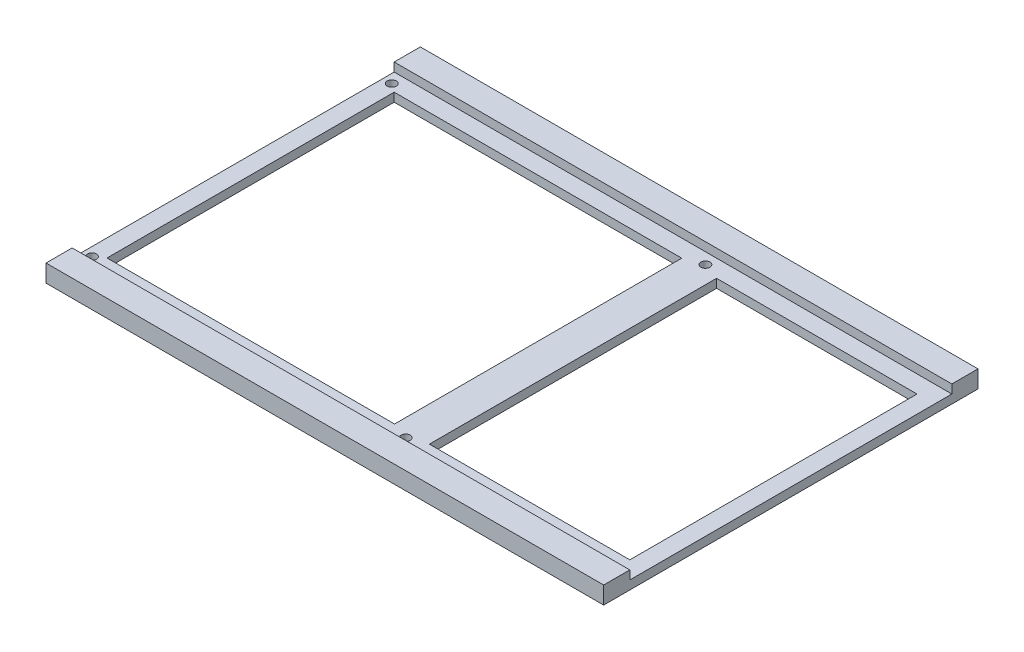
SolidWorks part; units mm, degrees
ref_plane "Front Plane" through (0, 0, 0) normal (0, 0, 1) x (1, 0, 0)
ref_plane "Top Plane" through (0, 0, 0) normal (0, 1, 0) x (1, 0, 0)
ref_plane "Right Plane" through (0, 0, 0) normal (1, 0, 0) x (0, 0, -1)
sketch "Sketch1" plane through (0, 0, 0) normal (0, 1, 0) x (1, 0, 0)
  line L1 (101.6, -68.199) -> (-101.6, -68.199)
  line L2 (101.6, -68.199) -> (101.6, 68.199)
  line L3 (101.6, 68.199) -> (-101.6, 68.199)
  line L4 (-101.6, -68.199) -> (-101.6, 68.199)
  line L5 (101.6, -68.199) -> (-101.6, 68.199) construction
  line L6 (101.6, 68.199) -> (-101.6, -68.199) construction
  point P0 (0, 0)
  dimension "D1" = 203.2
  dimension "D2" = 136.398
extrude "Boss-Extrude1" add sketch "Sketch1" along normal blind 6.35
sketch "Sketch3" plane through (101.6, 0, 0) normal (1, 0, 0) x (0, 0, -1)
  line L0 (-68.199, 6.35) -> (68.199, 6.35) construction
  line L1 (58.674, 3.175) -> (-58.674, 3.175)
  line L2 (58.674, 3.175) -> (58.674, 6.35)
  line L3 (58.674, 6.35) -> (-58.674, 6.35)
  line L4 (-58.674, 3.175) -> (-58.674, 6.35)
  line L5 (58.674, 3.175) -> (-58.674, 6.35) construction
  line L6 (58.674, 6.35) -> (-58.674, 3.175) construction
  line L7 (-68.199, 0) -> (68.199, 0) construction
  line L8 (-68.199, 6.35) -> (-68.199, 0) construction
  point P0 (0, 4.7625)
  point P10 (0, 0)
  dimension "D1" = 9.525
  dimension "D2" = 3.175
extrude "Cut-Extrude1" cut sketch "Sketch3" against normal through all
sketch "Sketch4" plane through (0, 3.175, 0) normal (0, 1, 0) x (1, 0, 0)
  line L1 (-101.6, -58.674) -> (-101.6, 58.674) construction
  line L2 (95.25, -52.324) -> (-95.25, -52.324)
  line L3 (95.25, -52.324) -> (95.25, 52.324)
  line L4 (95.25, 52.324) -> (-95.25, 52.324)
  line L5 (-95.25, -52.324) -> (-95.25, 52.324)
  line L6 (95.25, -52.324) -> (-95.25, 52.324) construction
  line L7 (95.25, 52.324) -> (-95.25, -52.324) construction
  line L8 (-101.6, 58.674) -> (101.6, 58.674) construction
  line L9 (22.225, -52.324) -> (22.225, 52.324)
  line L10 (9.525, -52.324) -> (9.525, 52.324)
  line L11 (-101.6, -11.9685) -> (-95.25, -11.9685) construction
  line L12 (9.525, 38.4482) -> (22.225, 38.4482) construction
  line L13 (15.875, 38.4482) -> (15.875, -96.3543) construction
  line L14 (-98.425, -11.9685) -> (-98.425, 16.517) construction
  point P0 (0, 0)
  dimension "D1" = 6.35
  dimension "D2" = 6.35
  dimension "D3" = 12.7
  dimension "D4" = 114.3
extrude "Cut-Extrude3" cut sketch "Sketch4" against normal through all contours L2 L10 L4 L5 | L9 L2 L3 L4
hole_wizard "M4x0.7 Tapped Hole1" positions "Sketch6" profile "Sketch5" tap size "M4x0.7" standard "ANSI Metric"
sketch "Sketch6" plane through (0, 3.175, 0) normal (0, 1, 0) x (1, 0, 0)
  line L0 (-98.425, -54.61) -> (-98.425, 54.61) construction
  line L2 (-95.25, -65.1111) -> (-101.6, -65.1111) construction
  line L3 (-95.25, -52.324) -> (-95.25, 52.324) construction
  line L4 (-101.6, -58.674) -> (-101.6, 58.674) construction
  line L5 (15.875, 54.61) -> (15.875, -54.61) construction
  line L7 (9.525, 0) -> (22.225, 0) construction
  line L8 (9.525, -52.324) -> (9.525, 52.324) construction
  line L9 (22.225, -52.324) -> (22.225, 52.324) construction
  point P0 (-98.425, -54.61)
  point P2 (-98.425, 54.61)
  point P9 (-98.425, 0)
  point P19 (-98.425, -65.1111)
  point P20 (15.875, 54.61)
  point P22 (15.875, -54.61)
  point P37 (15.875, 0)
  dimension "D1" = 109.22
sketch "Sketch5" plane through (-98.425, 3.175, 54.61) normal (1, 0, 0) x (0, 0, 1)
  line L0 (0, 0) -> (0, 9.906)
  line L1 (0, 9.906) -> (1.65, 9.906)
  line L2 (1.65, 9.906) -> (1.65, 0)
  line L5 (1.65, 0) -> (0, 0)
  line L10 (0, 9.906) -> (-1.65, 9.906) construction
  line L11 (0, -6.35) -> (0, 107.95) construction
  dimension "Tap Drill Dia." = 3.3
  dimension "Tap Drill Depth" = 9.906
  dimension "Drill Angle" = 180
cosmetic thread "Hole Thread5" parameters "D1"=3.175, "D2"=4
cosmetic thread "Hole Thread6" parameters "D1"=3.175, "D2"=4
cosmetic thread "Hole Thread7" parameters "D1"=3.175, "D2"=4
cosmetic thread "Hole Thread8" parameters "D1"=3.175, "D2"=4
